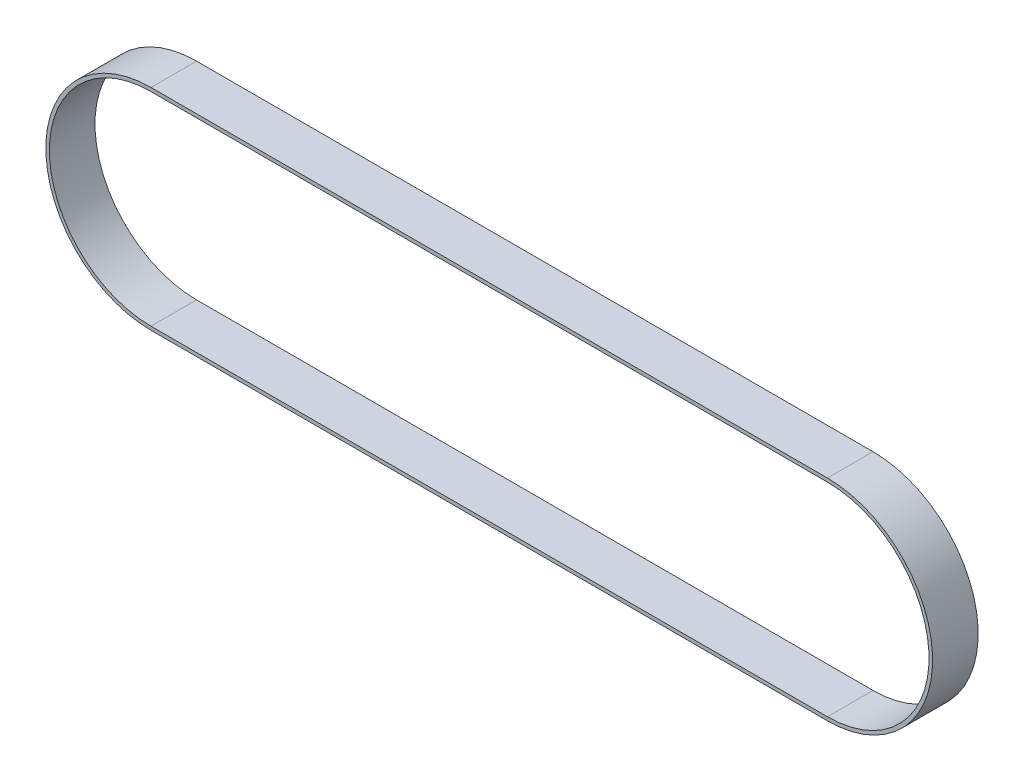
SolidWorks part; units mm, degrees
ref_plane "Front Plane" through (0, 0, 0) normal (0, 0, 1) x (1, 0, 0)
ref_plane "Top Plane" through (0, 0, 0) normal (0, 1, 0) x (1, 0, 0)
ref_plane "Right Plane" through (0, 0, 0) normal (1, 0, 0) x (0, 0, -1)
sketch "Sketch1" plane through (0, 0, 0) normal (0, 0, 1) x (1, 0, 0)
  line L0 (0, 33.4264) -> (222.5548, 33.4264)
  line L1 (0, -33.4264) -> (222.5548, -33.4264)
  line L2 (0, 34.5948) -> (222.5548, 34.5948)
  line L3 (0, -34.5948) -> (222.5548, -34.5948)
  arc A0 (0, 33.4264) -> (0, -33.4264) centre (0, 0) ccw
  arc A1 (222.5548, -33.4264) -> (222.5548, 33.4264) centre (222.5548, 0) ccw
  arc A2 (222.5548, -34.5948) -> (222.5548, 34.5948) centre (222.5548, 0) ccw
  arc A3 (0, 34.5948) -> (0, -34.5948) centre (0, 0) ccw
  dimension "D1" = 66.8528
  dimension "D2" = 222.5548
  dimension "D3" = 1.1684
extrude "Boss-Extrude1" add sketch "Sketch1" along normal blind 15
